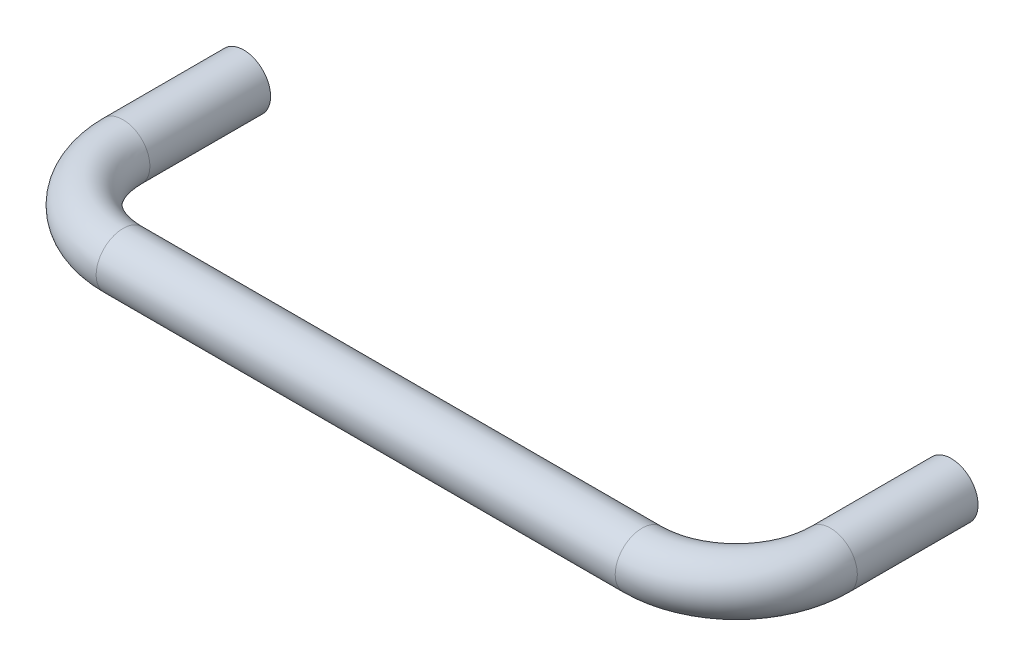
SolidWorks part; units mm, degrees
material "IMPERIAL HARDWARE"
ref_plane "Front Plane" through (0, 0, 0) normal (0, 0, 1) x (1, 0, 0)
ref_plane "Top Plane" through (0, 0, 0) normal (0, 1, 0) x (1, 0, 0)
ref_plane "Right Plane" through (0, 0, 0) normal (1, 0, 0) x (0, 0, -1)
sketch "Sketch1" plane through (0, 0, 0) normal (0, 1, 0) x (1, 0, 0)
  line L0 (46.0058, -19.05) -> (46.0058, 0) construction
  line L1 (-62.7063, 19.05) -> (62.7063, 19.05) construction
  line L2 (-62.7063, 19.05) -> (-62.7063, -2.3495)
  line L3 (-46.0058, -19.05) -> (46.0058, -19.05)
  line L4 (62.7063, 19.05) -> (62.7063, -2.3495)
  line L5 (-67.4688, 19.05) -> (-57.9438, 19.05) construction
  line L6 (-57.9438, 19.05) -> (-57.9438, -2.3495) construction
  line L7 (-46.0058, -14.2875) -> (46.0058, -14.2875) construction
  line L8 (-64.2303, 13.97) -> (-61.1823, 13.97) construction
  line L9 (57.9438, 19.05) -> (57.9438, -2.3495) construction
  line L10 (0, -14.2875) -> (0, -23.8125) construction
  line L11 (46.0058, 0) -> (46.0058, 19.05) construction
  line L12 (-61.1823, 13.97) -> (-62.7063, 13.0901) construction
  line L13 (-62.7063, 13.0901) -> (-64.2303, 13.97) construction
  line L14 (-64.2303, 13.97) -> (-64.2303, 19.05) construction
  line L15 (-61.1823, 13.97) -> (-61.1823, 19.05) construction
  line L16 (64.2303, 13.97) -> (64.2303, 19.05) construction
  line L17 (61.1823, 13.97) -> (61.1823, 19.05) construction
  line L18 (61.1823, 13.97) -> (62.7063, 13.0901) construction
  line L19 (62.7063, 13.0901) -> (64.2303, 13.97) construction
  arc A0 (46.0058, -19.05) -> (62.7063, -2.3495) centre (46.0058, -2.3495) ccw
  arc A1 (-62.7063, -2.3495) -> (-46.0058, -19.05) centre (-46.0058, -2.3495) ccw
  arc A2 (-57.9438, -2.3495) -> (-46.0058, -14.2875) centre (-46.0058, -2.3495) ccw construction
  arc A3 (46.0058, -14.2875) -> (57.9438, -2.3495) centre (46.0058, -2.3495) ccw construction
  point P14 (-62.7063, 13.97)
  point P24 (0, -19.05)
  dimension "D1" = 30
  dimension "r" = 11.938
  dimension "Width" = 125.4125
  dimension "Grip Dia" = 9.525
  dimension "Grip Height" = 42.8625
  dimension "t" = 5.08
  dimension "Pin Dia" = 3.048
ref_plane "Profile Plane" through (0, 0, -19.05) normal (0, 0, 1) x (1, 0, 0)
sketch "Sketch2" plane through (0, 0, -19.05) normal (0, 0, 1) x (1, 0, 0)
  circle A0 centre (-62.7063, 0) radius 4.7625
sketch "Sketch3" plane through (0, 0, 0) normal (0, 1, 0) x (1, 0, 0)
  line L0 (62.7063, 19.05) -> (62.7063, -2.3495) construction
  line L1 (-46.0058, -19.05) -> (46.0058, -19.05) construction
  line L2 (-62.7063, 19.05) -> (-62.7063, -2.3495) construction
  line L3 (62.7063, 19.05) -> (62.7063, -2.3495)
  line L4 (-46.0058, -19.05) -> (46.0058, -19.05)
  line L5 (-62.7063, 19.05) -> (-62.7063, -2.3495)
  arc A0 (46.0058, -19.05) -> (62.7063, -2.3495) centre (46.0058, -2.3495) ccw construction
  arc A1 (-62.7063, -2.3495) -> (-46.0058, -19.05) centre (-46.0058, -2.3495) ccw construction
  arc A2 (46.0058, -19.05) -> (62.7063, -2.3495) centre (46.0058, -2.3495) ccw
  arc A3 (-62.7063, -2.3495) -> (-46.0058, -19.05) centre (-46.0058, -2.3495) ccw
sweep "Handle" add profiles "Sketch2" path "Sketch3"
sketch "Sketch4" plane through (0, 0, -19.05) normal (0, 0, -1) x (-1, 0, 0)
  circle A0 centre (62.7063, 0) radius 1.524
  circle A1 centre (-62.7063, 0) radius 1.524
  point P3 (64.2303, 0)
extrude "Location Hole" cut sketch "Sketch4" against normal blind 2.54 draft 60 and the other way through all from vertex at -5.08
sketch "Sketch5" plane through (0, 0, 0) normal (0, 1, 0) x (1, 0, 0)
  line L0 (-62.7063, 13.0901) -> (-64.2303, 13.97) construction
  line L1 (-61.1823, 13.97) -> (-62.7063, 13.0901) construction
  line L2 (-61.1823, 13.97) -> (-61.1823, 19.05) construction
  line L3 (-64.2303, 13.97) -> (-64.2303, 19.05) construction
  line L4 (61.1823, 13.97) -> (61.1823, 19.05) construction
  line L5 (64.2303, 13.97) -> (64.2303, 19.05) construction
  line L6 (62.7063, 13.0901) -> (64.2303, 13.97) construction
  line L7 (61.1823, 13.97) -> (62.7063, 13.0901) construction
  line L8 (-62.7063, 13.0901) -> (-64.2303, 13.97)
  line L9 (-61.1823, 13.97) -> (-62.7063, 13.0901)
  line L10 (-61.1823, 13.97) -> (-61.1823, 19.05)
  line L11 (-64.2303, 13.97) -> (-64.2303, 19.05)
  line L12 (61.1823, 13.97) -> (61.1823, 19.05)
  line L13 (64.2303, 13.97) -> (64.2303, 19.05)
  line L14 (62.7063, 13.0901) -> (64.2303, 13.97)
  line L15 (61.1823, 13.97) -> (62.7063, 13.0901)
